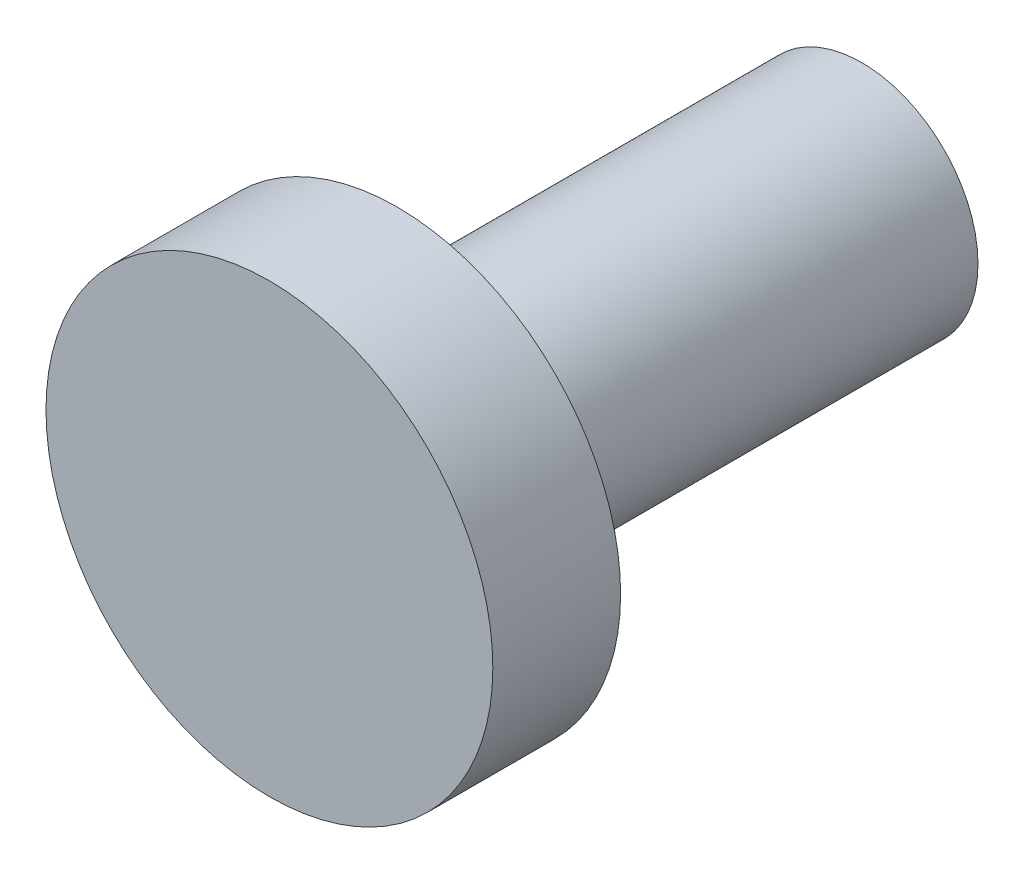
SolidWorks part; units mm, degrees
ref_plane "Alzado" through (0, 0, 0) normal (0, 0, 1) x (1, 0, 0)
ref_plane "Planta" through (0, 0, 0) normal (0, 1, 0) x (1, 0, 0)
ref_plane "Vista lateral" through (0, 0, 0) normal (1, 0, 0) x (0, 0, -1)
sketch "0" plane through (0, 0, 0) normal (0, 0, 1) x (1, 0, 0)
  circle A0 centre (33.9083, 19.9167) radius 2.885
sketch "Corte exterior" plane through (0, 0, 0) normal (0, 0, 1) x (1, 0, 0)
  circle A0 centre (33.9083, 19.9167) radius 1.5
extrude "Saliente-Extruir1" add sketch "0" along normal blind 1.65
extrude "Saliente-Extruir2" add sketch "Corte exterior" against normal blind 6
